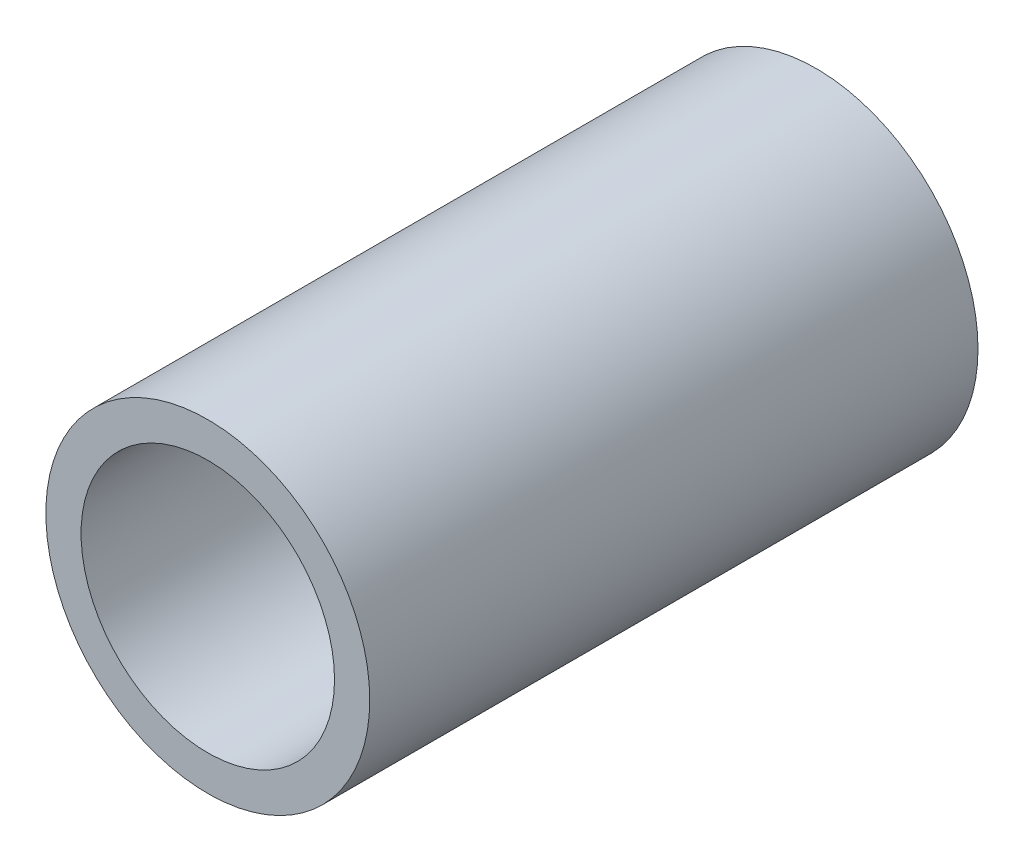
SolidWorks part; units mm, degrees
ref_plane "Front Plane" through (0, 0, 0) normal (0, 0, 1) x (1, 0, 0)
ref_plane "Top Plane" through (0, 0, 0) normal (0, 1, 0) x (1, 0, 0)
ref_plane "Right Plane" through (0, 0, 0) normal (1, 0, 0) x (0, 0, -1)
sketch "Sketch1" plane through (0, 0, 0) normal (0, 0, 1) x (1, 0, 0)
  circle A0 centre (-7.4735, 0) radius 15.975
  circle A1 centre (-7.4735, 0) radius 12.5
extrude "Boss-Extrude1" add sketch "Sketch1" along normal blind 60
